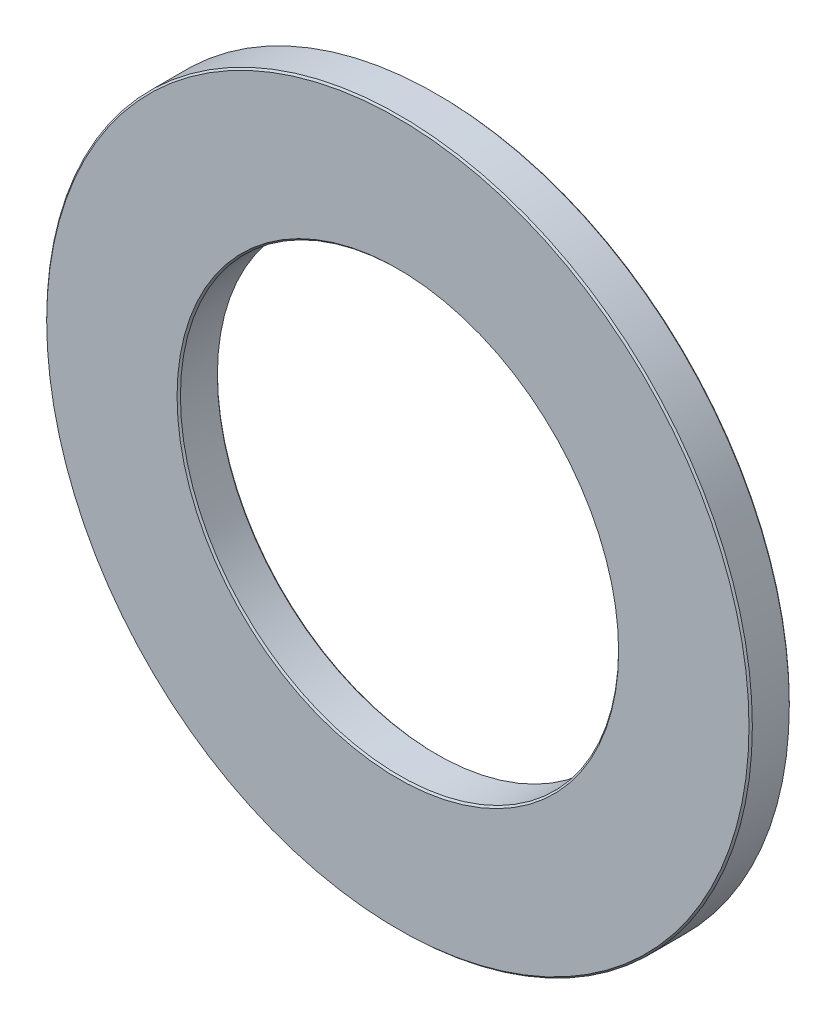
SolidWorks part; units mm, degrees
ref_plane "Front Plane" through (0, 0, 0) normal (0, 0, 1) x (1, 0, 0)
ref_plane "Top Plane" through (0, 0, 0) normal (0, 1, 0) x (1, 0, 0)
ref_plane "Right Plane" through (0, 0, 0) normal (1, 0, 0) x (0, 0, -1)
sketch "Sketch1" plane through (0, 0, 0) normal (0, 0, 1) x (1, 0, 0)
  circle A0 centre (0, 0) radius 52.5
  circle A1 centre (0, 0) radius 32.6
  dimension "D1" = 65.2
  dimension "D2" = 105
extrude "Boss-Extrude1" add sketch "Sketch1" along normal blind 6
chamfer "Chamfer1" distance 0.25 4 edges at (32.6, 0, 0) (32.6, 0, 6) (52.5, 0, 0) (52.5, 0, 6)
